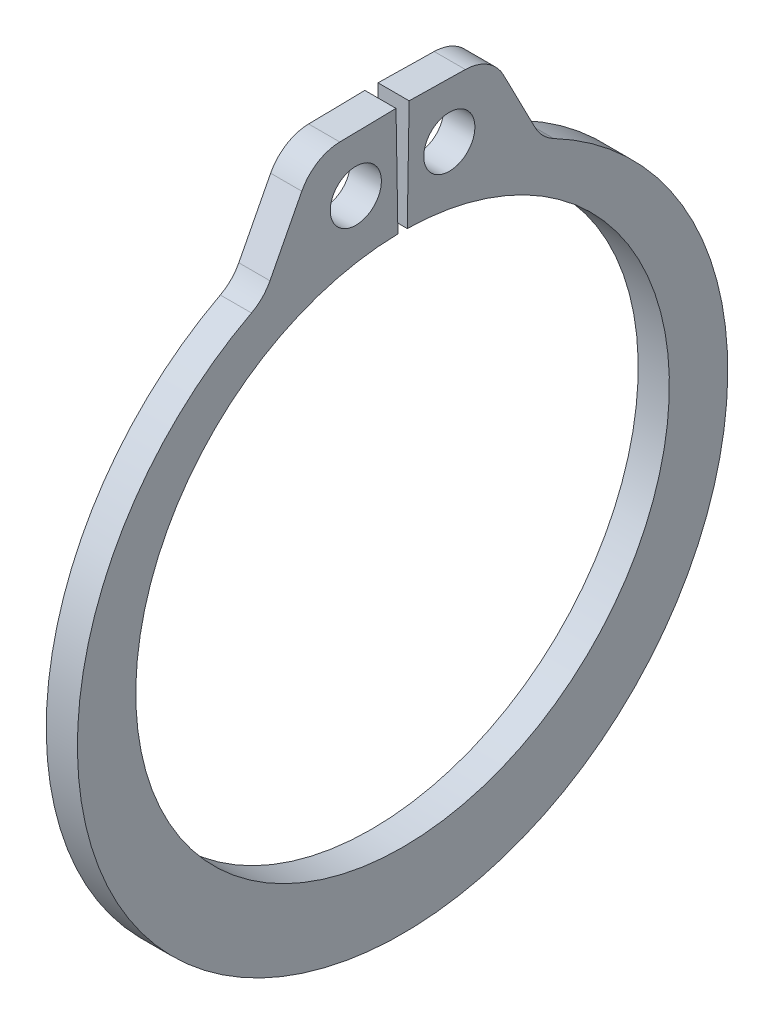
SolidWorks part; units mm, degrees
material "Cast Carbon Steel"
ref_plane "Front" through (0, 0, 0) normal (0, 0, 1) x (1, 0, 0)
ref_plane "Top" through (0, 0, 0) normal (0, 1, 0) x (1, 0, 0)
ref_plane "Right" through (0, 0, 0) normal (1, 0, 0) x (0, 0, -1)
sketch "Sketch1" plane through (0, 0, 0) normal (1, 0, 0) x (0, 0, -1)
  line L0 (0, 0) -> (0, 5.4356) construction
  line L1 (-0.0949, 5.4348) -> (-0.1339, 7.6696)
  line L2 (0.1339, 7.6696) -> (1.81, 7.6404)
  line L3 (1.81, 7.6404) -> (2.8346, 5.6538)
  line L4 (0.0949, 5.4348) -> (0.1339, 7.6696)
  line L5 (-0.1339, 7.6696) -> (-1.81, 7.6404)
  line L6 (-1.81, 7.6404) -> (-2.8346, 5.6538)
  line L7 (-2.8346, 5.6538) -> (-2.4361, 4.8591) construction
  line L8 (2.8346, 5.6538) -> (2.4361, 4.8591) construction
  line L9 (0, -5.4356) -> (0, -6.9596) construction
  line L10 (-1.81, 7.6404) -> (-0.0949, 5.4348) construction
  line L11 (0, 5.4356) -> (0, 7.6708) construction
  line L12 (-5.4356, 0) -> (5.4356, 0) construction
  circle A0 centre (0, 0) radius 5.4356 construction
  arc A1 (-0.0949, 5.4348) -> (0.0949, 5.4348) centre (0, 0) ccw
  circle A3 centre (0, 0) radius 8.509 construction
  circle A4 centre (-0.9524, 6.5376) radius 0.5207
  circle A5 centre (0.9524, 6.5376) radius 0.5207
  arc A6 (-2.8346, 5.6538) -> (2.8346, 5.6538) centre (0, -0.3344) ccw
  point P0 (0, -6.9596)
  dimension "A" = 10.8712
  dimension "Hole" = 1.0414
  dimension "Smin" = 0.889
  dimension "H" = 2.2352
  dimension "D2" = 1.6764
  dimension "Angle" = 1
extrude "Extrude1" add sketch "Sketch1" along normal mid plane 0.635
fillet "Fillet1" radius 0.889 4 edges at (0, 5.6538, 2.8346) (0, 5.6538, -2.8346) (0, 7.6404, 1.81) (0, 7.6404, -1.81)
sketch "Sketch2" plane through (0, 0, 0) normal (0, 0, 1) x (1, 0, 0)
  line L0 (-3.5433, 0) -> (9.1567, 0)
  line L1 (9.1567, 0) -> (9.1567, -5.9563)
  line L2 (-0.3683, -5.9563) -> (-3.2131, -5.9563)
  line L3 (9.1567, -5.9563) -> (0.3683, -5.9563)
  line L4 (0.3683, -5.9563) -> (0.3683, -5.6261)
  line L5 (0.3683, -5.6261) -> (-0.3683, -5.6261)
  line L6 (-0.3683, -5.6261) -> (-0.3683, -5.9563)
  line L7 (-0.3683, -5.9563) -> (-3.5433, -5.9563) construction
  line L8 (-3.5433, -5.9563) -> (-3.5433, 0) construction
  line L9 (9.1567, 0) -> (76.391, 0) construction
  line L10 (-3.2131, -5.9563) -> (-3.5433, -5.6261)
  line L11 (-3.5433, -5.6261) -> (-3.5433, 0)
  point P10 (0, -5.6261)
  dimension "Dg" = 11.2522
  dimension "Ds" = 11.9126
  dimension "D2" = 12.7
  dimension "D3" = 3.175
  dimension "D1" = 45
equation "\"D2@Sketch2\" = \"D1@Extrude1\"*20"
equation "\"D3@Sketch2\" = \"D2@Sketch2\"/4"
equation "\"D2@Sketch1\" = \"H@Sketch1\"*.75"
